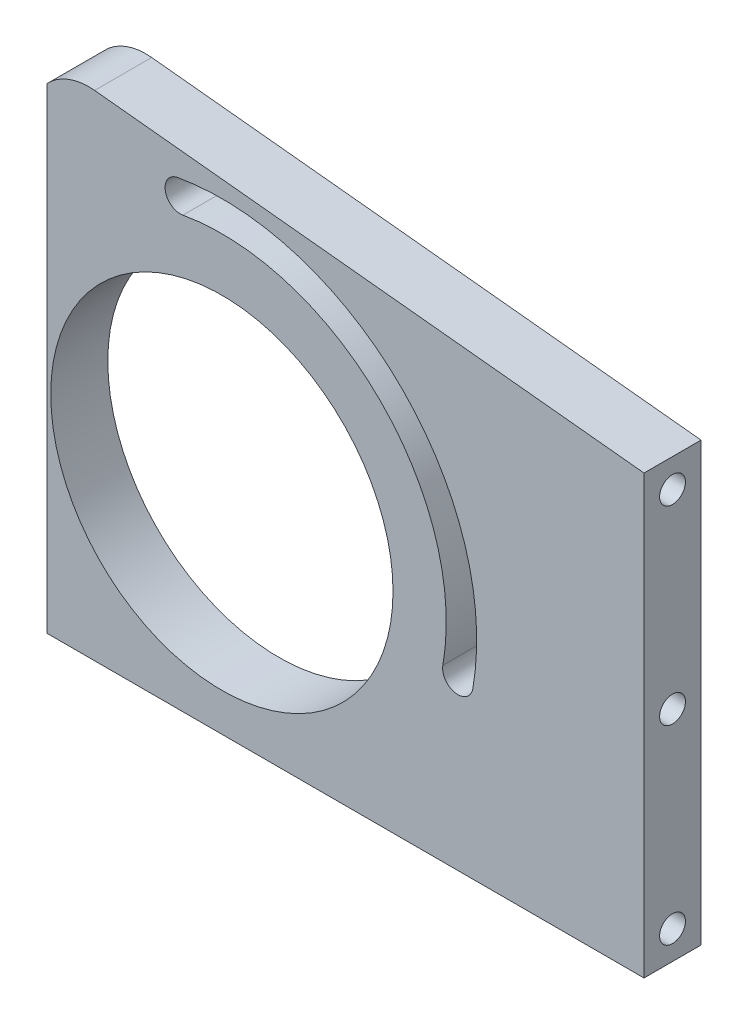
SolidWorks part; units mm, degrees
ref_plane "Alzado" through (0, 0, 0) normal (0, 0, 1) x (1, 0, 0)
ref_plane "Planta" through (0, 0, 0) normal (0, 1, 0) x (1, 0, 0)
ref_plane "Vista lateral" through (0, 0, 0) normal (1, 0, 0) x (0, 0, -1)
sketch "Croquis1" plane through (0, 0, 0) normal (0, 0, 1) x (1, 0, 0)
  line L0 (-50, -55) -> (-50, 59.9739)
  line L1 (-33.4616, 74.8948) -> (111, 60)
  line L2 (111, 60) -> (111, -55)
  line L3 (111, -55) -> (-50, -55)
  line L4 (-10.9398, 62.0429) -> (0, 0) construction
  line L5 (0, 81.6267) -> (0, -95.7741) construction
  line L6 (-57.2433, 0) -> (134.3181, 0) construction
  line L7 (0, 0) -> (62.0429, -10.9398) construction
  circle A0 centre (0, 0) radius 45
  arc A1 (-50, 59.9739) -> (-33.4616, 74.8948) centre (-35, 59.9739) cw
  arc A2 (-10.9398, 62.0429) -> (62.0429, -10.9398) centre (0, 0) cw construction
  arc A3 (65.9821, -11.6344) -> (-11.6344, 65.9821) centre (0, 0) ccw
  arc A4 (58.1037, -10.2452) -> (-10.2452, 58.1037) centre (0, 0) ccw
  arc A5 (58.1037, -10.2452) -> (65.9821, -11.6344) centre (62.0429, -10.9398) ccw
  arc A6 (-11.6344, 65.9821) -> (-10.2452, 58.1037) centre (-10.9398, 62.0429) ccw
  point P9 (-50, 76.6)
  point P12 (44.5477, 44.5477)
  dimension "D1" = 90
  dimension "D7" = 15
  dimension "D8" = 63
  dimension "D9" = 8
  dimension "D2" = 50
  dimension "D3" = 111
  dimension "D4" = 131.6
  dimension "D5" = 115
  dimension "D6" = 55
  dimension "D10" = 10
  dimension "D11" = 10
extrude "Saliente-Extruir1" add sketch "Croquis1" along normal mid plane 15
hole_wizard "Taladro roscado M81" positions "Croquis3" profile "Croquis2" tap size "M8" standard "DIN"
sketch "Croquis3" plane through (111, 0, 0) normal (1, 0, 0) x (0, 0, -1)
  line L0 (-7.5, -55) -> (7.5, -55) construction
  point P0 (0, 52.5)
  point P1 (0, 2.5)
  point P4 (0, -47.5)
  dimension "D1" = 50
  dimension "D2" = 50
  dimension "D3" = 7.5
sketch "Croquis2" plane through (111, 52.5, 0) normal (0, 1, 0) x (0, 0, -1)
  line L0 (0, 0) -> (0, 22.0429)
  line L1 (0, 22.0429) -> (3.4, 20)
  line L2 (3.4, 20) -> (3.4, 0)
  line L5 (3.4, 0) -> (0, 0)
  line L10 (0, 22.0429) -> (-3.4, 20) construction
  line L11 (0, -6.35) -> (0, 107.95) construction
  dimension "Diámetro de perforador para roscar" = 6.8
  dimension "Profundidad de perforador para roscar" = 20
  dimension "Ángulo de perforador" = 118
cosmetic thread "Rosca de taladro1" parameters "D1"=16, "D2"=8
cosmetic thread "Rosca de taladro2" parameters "D1"=16, "D2"=8
cosmetic thread "Rosca de taladro3" parameters "D1"=16, "D2"=8
hole_wizard "Taladro roscado M82" positions "Croquis6" profile "Croquis5" tap size "M8" standard "DIN"
sketch "Croquis6" plane through (0, -55, 0) normal (0, -1, 0) x (1, 0, 0)
  line L0 (-50, 7.5) -> (-50, -7.5) construction
  point P0 (-42.5, 0)
  point P1 (16.3, 0)
  point P3 (75.1, 0)
  dimension "D1" = 7.5
  dimension "D2" = 58.8
  dimension "D3" = 58.8
sketch "Croquis5" plane through (-42.5, -55, 0) normal (1, 0, 0) x (0, 0, -1)
  line L0 (0, 0) -> (0, 12.0429)
  line L1 (0, 12.0429) -> (3.4, 10)
  line L2 (3.4, 10) -> (3.4, 0)
  line L5 (3.4, 0) -> (0, 0)
  line L10 (0, 12.0429) -> (-3.4, 10) construction
  line L11 (0, -6.35) -> (0, 107.95) construction
  dimension "Diámetro de perforador para roscar" = 6.8
  dimension "Profundidad de perforador para roscar" = 10
  dimension "Ángulo de perforador" = 118
cosmetic thread "Rosca de taladro4" parameters "D1"=10, "D2"=8
cosmetic thread "Rosca de taladro5" parameters "D1"=10, "D2"=8
cosmetic thread "Rosca de taladro6" parameters "D1"=10, "D2"=8
sketch "Croquis7" plane through (0, -55, 0) normal (0, -1, 0) x (1, 0, 0)
  line L0 (-50, 7.5) -> (-50, 3.5)
  line L1 (-50, 7.5) -> (-50, -7.5) construction
  line L2 (-50, 3.5) -> (-46, 7.5)
  line L3 (-50, 7.5) -> (111, 7.5) construction
  line L4 (-46, 7.5) -> (-50, 7.5)
  line L5 (-50, -7.5) -> (-50, -3.5)
  line L6 (-50, -3.5) -> (-46, -7.5)
  line L7 (-50, -7.5) -> (111, -7.5) construction
  line L8 (-46, -7.5) -> (-50, -7.5)
  dimension "D1" = 4
  dimension "D2" = 4
  dimension "D3" = 4
  dimension "D4" = 4
extrude "Cortar-Extruir1" cut sketch "Croquis7" against normal blind 167.9
